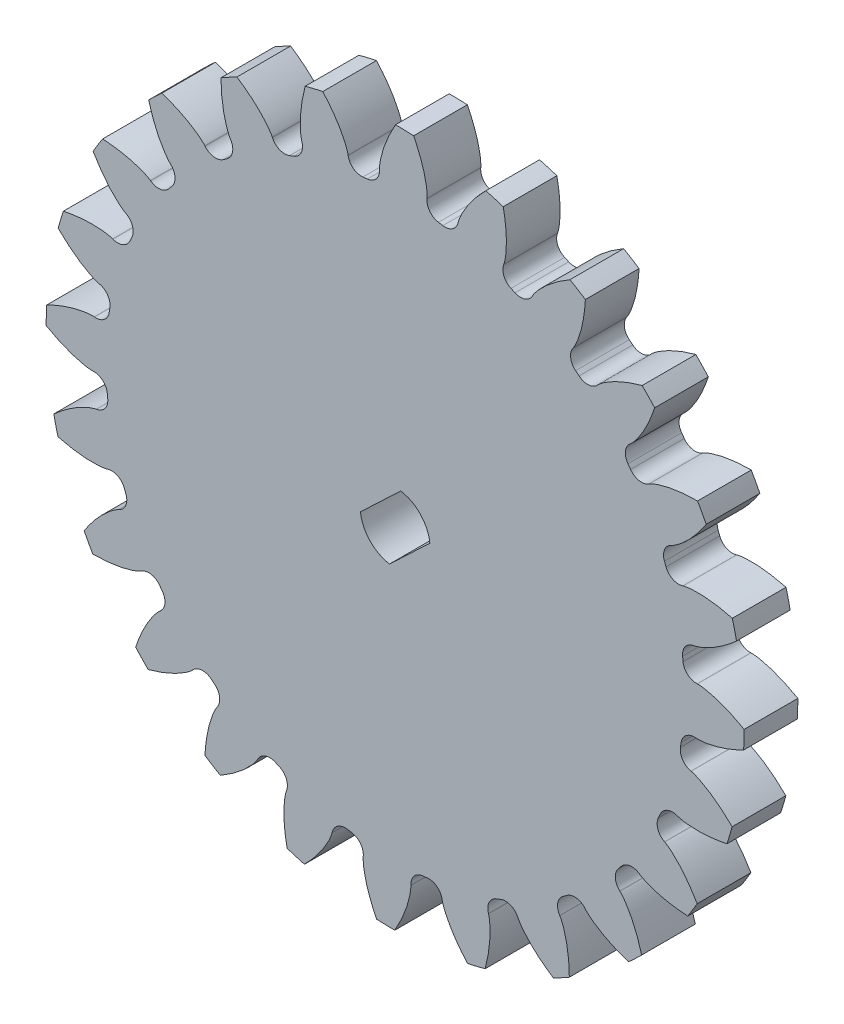
SolidWorks part; units mm, degrees
ref_plane "Plano frontal" through (0, 0, 0) normal (0, 0, 1) x (1, 0, 0)
ref_plane "Plano superior" through (0, 0, 0) normal (0, 1, 0) x (1, 0, 0)
ref_plane "Plano direito" through (0, 0, 0) normal (1, 0, 0) x (0, 0, -1)
sketch "Model" plane through (0, 0, 0) normal (0, 0, 1) x (1, 0, 0)
  line L0 (-21.0216, 0.4198) -> (-21.0462, 0.4292)
  line L1 (-22.0572, -2.974) -> (-22.0314, -2.9795)
  line L2 (-22.4004, -5.2968) -> (-22.4266, -5.2941)
  line L3 (-22.5224, -8.843) -> (-22.496, -8.8417)
  line L4 (-22.2526, -11.1755) -> (-22.2787, -11.1796)
  line L5 (-21.4526, -14.6324) -> (-21.4275, -14.6243)
  line L6 (-20.5884, -16.8156) -> (-20.6125, -16.8263)
  line L7 (-18.9209, -19.9477) -> (-18.8988, -19.9334)
  line L8 (-17.5211, -21.8328) -> (-17.5416, -21.8494)
  line L9 (-15.0998, -24.4266) -> (-15.0821, -24.407)
  line L10 (-13.2597, -25.8852) -> (-13.2752, -25.9065)
  line L11 (-10.2496, -27.7639) -> (-10.2376, -27.7404)
  line L12 (-8.0948, -28.6966) -> (-8.1042, -28.7212)
  line L13 (-4.701, -29.7322) -> (-4.6955, -29.7064)
  line L14 (-2.3782, -30.0754) -> (-2.3809, -30.1016)
  line L15 (1.168, -30.1974) -> (1.1667, -30.171)
  line L16 (3.5005, -29.9276) -> (3.5046, -29.9537)
  line L17 (6.9574, -29.1276) -> (6.9493, -29.1025)
  line L18 (9.1406, -28.2634) -> (9.1513, -28.2875)
  line L19 (12.2727, -26.5959) -> (12.2584, -26.5738)
  line L20 (14.1578, -25.1961) -> (14.1744, -25.2166)
  line L21 (16.7516, -22.7748) -> (16.732, -22.7571)
  line L22 (18.2102, -20.9347) -> (18.2315, -20.9502)
  line L23 (20.0889, -17.9246) -> (20.0654, -17.9126)
  line L24 (21.0216, -15.7698) -> (21.0462, -15.7792)
  line L25 (22.0572, -12.376) -> (22.0314, -12.3705)
  line L26 (22.4004, -10.0532) -> (22.4266, -10.0559)
  line L27 (22.5224, -6.507) -> (22.496, -6.5083)
  line L28 (22.2526, -4.1745) -> (22.2787, -4.1704)
  line L29 (21.4526, -0.7176) -> (21.4275, -0.7257)
  line L30 (20.5884, 1.4656) -> (20.6125, 1.4763)
  line L31 (18.9209, 4.5977) -> (18.8988, 4.5834)
  line L32 (17.5211, 6.4828) -> (17.5416, 6.4994)
  line L33 (15.0998, 9.0766) -> (15.0821, 9.057)
  line L34 (13.2597, 10.5352) -> (13.2752, 10.5565)
  line L35 (10.2496, 12.4139) -> (10.2376, 12.3904)
  line L36 (8.0948, 13.3466) -> (8.1042, 13.3712)
  line L37 (4.701, 14.3822) -> (4.6955, 14.3564)
  line L38 (2.3782, 14.7254) -> (2.3809, 14.7516)
  line L39 (-1.168, 14.8474) -> (-1.1667, 14.821)
  line L40 (-3.5005, 14.5776) -> (-3.5046, 14.6037)
  line L41 (-6.9574, 13.7776) -> (-6.9493, 13.7525)
  line L42 (-9.1406, 12.9134) -> (-9.1513, 12.9375)
  line L43 (-12.2727, 11.2459) -> (-12.2584, 11.2238)
  line L44 (-14.1578, 9.8461) -> (-14.1744, 9.8666)
  line L45 (-16.7516, 7.4248) -> (-16.732, 7.4071)
  line L46 (-18.2102, 5.5847) -> (-18.2315, 5.6002)
  line L47 (-20.0889, 2.5746) -> (-20.0654, 2.5626)
  line L48 (-0.4184, -10.2411) -> (2.5849, -7.3956)
  line L49 (0.4184, -5.1089) -> (-2.5849, -7.9544)
  arc A0 (-19.6106, 1.2577) -> (-19.7466, 0.9529) centre (0, -7.675) ccw
  arc A1 (-21.0216, 0.4198) -> (-19.7466, 0.9529) centre (-20.6629, 1.3533) ccw
  arc A2 (-24.7228, 0.3737) -> (-25.1072, -0.9201) centre (0, -7.675) ccw
  arc A3 (-21.2543, -4.1223) -> (-22.0314, -2.9795) centre (-22.2406, -3.9574) ccw
  arc A4 (-21.2543, -4.1223) -> (-21.3068, -4.4519) centre (0, -7.675) ccw
  arc A5 (-22.4004, -5.2968) -> (-21.3068, -4.4519) centre (-22.2955, -4.3023) ccw
  arc A6 (-25.9636, -6.2993) -> (-26, -7.6485) centre (0, -7.675) ccw
  arc A7 (-21.4496, -9.7443) -> (-22.496, -8.8417) centre (-22.445, -9.8404) ccw
  arc A8 (-21.4496, -9.7443) -> (-21.415, -10.0763) centre (0, -7.675) ccw
  arc A9 (-22.2526, -11.1755) -> (-21.415, -10.0763) centre (-22.4088, -10.1878) ccw
  arc A10 (-25.435, -13.066) -> (-25.1209, -14.3787) centre (0, -7.675) ccw
  arc A11 (-20.1832, -15.2254) -> (-21.4275, -14.6243) centre (-21.1198, -15.5758) ccw
  arc A12 (-20.1832, -15.2254) -> (-20.0638, -15.5371) centre (0, -7.675) ccw
  arc A13 (-20.5884, -16.8156) -> (-20.0638, -15.5371) centre (-20.9948, -15.902) ccw
  arc A14 (-23.173, -19.4654) -> (-22.5299, -20.652) centre (0, -7.675) ccw
  arc A15 (-17.5412, -20.1919) -> (-18.8988, -19.9334) centre (-18.3552, -20.7728) ccw
  arc A16 (-17.5412, -20.1919) -> (-17.3453, -20.4621) centre (0, -7.675) ccw
  arc A17 (-17.5211, -21.8328) -> (-17.3453, -20.4621) centre (-18.1502, -21.0555) ccw
  arc A18 (-19.3318, -25.0613) -> (-18.4035, -26.041) centre (0, -7.675) ccw
  arc A19 (-13.7039, -24.3054) -> (-15.0821, -24.407) centre (-14.3399, -25.0772) ccw
  arc A20 (-13.7039, -24.3054) -> (-13.4447, -24.5157) centre (0, -7.675) ccw
  arc A21 (-13.2597, -25.8852) -> (-13.4447, -24.5157) centre (-14.0686, -25.2972) ccw
  arc A22 (-14.1732, -29.4723) -> (-13.0229, -30.1784) centre (0, -7.675) ccw
  arc A23 (-8.9327, -27.2856) -> (-10.2376, -27.7404) centre (-9.3472, -28.1956) ccw
  arc A24 (-8.9327, -27.2856) -> (-8.6279, -27.4216) centre (0, -7.675) ccw
  arc A25 (-8.0948, -28.6966) -> (-8.6279, -27.4216) centre (-9.0283, -28.3379) ccw
  arc A26 (-8.0487, -32.3978) -> (-6.7549, -32.7822) centre (0, -7.675) ccw
  arc A27 (-3.5527, -28.9293) -> (-4.6955, -29.7064) centre (-3.7176, -29.9156) ccw
  arc A28 (-3.5527, -28.9293) -> (-3.2231, -28.9818) centre (0, -7.675) ccw
  arc A29 (-2.3782, -30.0754) -> (-3.2231, -28.9818) centre (-3.3727, -29.9705) ccw
  arc A30 (-1.3757, -33.6386) -> (-0.0265, -33.675) centre (0, -7.675) ccw
  arc A31 (2.0693, -29.1246) -> (1.1667, -30.171) centre (2.1654, -30.12) ccw
  arc A32 (2.0693, -29.1246) -> (2.4013, -29.09) centre (0, -7.675) ccw
  arc A33 (3.5005, -29.9276) -> (2.4013, -29.09) centre (2.5128, -30.0838) ccw
  arc A34 (5.391, -33.11) -> (6.7037, -32.7959) centre (0, -7.675) ccw
  arc A35 (7.5504, -27.8581) -> (6.9493, -29.1025) centre (7.9008, -28.7948) ccw
  arc A36 (7.5504, -27.8581) -> (7.8621, -27.7388) centre (0, -7.675) ccw
  arc A37 (9.1406, -28.2634) -> (7.8621, -27.7388) centre (8.227, -28.6698) ccw
  arc A38 (11.7904, -30.848) -> (12.977, -30.2049) centre (0, -7.675) ccw
  arc A39 (12.5169, -25.2162) -> (12.2584, -26.5738) centre (13.0978, -26.0302) ccw
  arc A40 (12.5169, -25.2162) -> (12.7871, -25.0203) centre (0, -7.675) ccw
  arc A41 (14.1578, -25.1961) -> (12.7871, -25.0203) centre (13.3805, -25.8252) ccw
  arc A42 (17.3863, -27.0068) -> (18.366, -26.0785) centre (0, -7.675) ccw
  arc A43 (16.6304, -21.3789) -> (16.732, -22.7571) centre (17.4022, -22.0149) ccw
  arc A44 (16.6304, -21.3789) -> (16.8407, -21.1197) centre (0, -7.675) ccw
  arc A45 (18.2102, -20.9347) -> (16.8407, -21.1197) centre (17.6222, -21.7436) ccw
  arc A46 (21.7973, -21.8482) -> (22.5034, -20.6979) centre (0, -7.675) ccw
  arc A47 (19.6106, -16.6077) -> (20.0654, -17.9126) centre (20.5206, -17.0222) ccw
  arc A48 (19.6106, -16.6077) -> (19.7466, -16.3029) centre (0, -7.675) ccw
  arc A49 (21.0216, -15.7698) -> (19.7466, -16.3029) centre (20.6629, -16.7033) ccw
  arc A50 (24.7228, -15.7237) -> (25.1072, -14.4299) centre (0, -7.675) ccw
  arc A51 (21.2543, -11.2277) -> (22.0314, -12.3705) centre (22.2406, -11.3926) ccw
  arc A52 (21.2543, -11.2277) -> (21.3068, -10.8981) centre (0, -7.675) ccw
  arc A53 (22.4004, -10.0532) -> (21.3068, -10.8981) centre (22.2955, -11.0477) ccw
  arc A54 (25.9636, -9.0507) -> (26, -7.7015) centre (0, -7.675) ccw
  arc A55 (21.4496, -5.6057) -> (22.496, -6.5083) centre (22.445, -5.5096) ccw
  arc A56 (21.4496, -5.6057) -> (21.415, -5.2737) centre (0, -7.675) ccw
  arc A57 (22.2526, -4.1745) -> (21.415, -5.2737) centre (22.4088, -5.1622) ccw
  arc A58 (25.435, -2.284) -> (25.1209, -0.9713) centre (0, -7.675) ccw
  arc A59 (20.1832, -0.1246) -> (21.4275, -0.7257) centre (21.1198, 0.2258) ccw
  arc A60 (20.1832, -0.1246) -> (20.0638, 0.1871) centre (0, -7.675) ccw
  arc A61 (20.5884, 1.4656) -> (20.0638, 0.1871) centre (20.9948, 0.552) ccw
  arc A62 (23.173, 4.1154) -> (22.5299, 5.302) centre (0, -7.675) ccw
  arc A63 (17.5412, 4.8419) -> (18.8988, 4.5834) centre (18.3552, 5.4228) ccw
  arc A64 (17.5412, 4.8419) -> (17.3453, 5.1121) centre (0, -7.675) ccw
  arc A65 (17.5211, 6.4828) -> (17.3453, 5.1121) centre (18.1502, 5.7055) ccw
  arc A66 (19.3318, 9.7113) -> (18.4035, 10.691) centre (0, -7.675) ccw
  arc A67 (13.7039, 8.9554) -> (15.0821, 9.057) centre (14.3399, 9.7272) ccw
  arc A68 (13.7039, 8.9554) -> (13.4447, 9.1657) centre (0, -7.675) ccw
  arc A69 (13.2597, 10.5352) -> (13.4447, 9.1657) centre (14.0686, 9.9472) ccw
  arc A70 (14.1732, 14.1223) -> (13.0229, 14.8284) centre (0, -7.675) ccw
  arc A71 (8.9327, 11.9356) -> (10.2376, 12.3904) centre (9.3472, 12.8456) ccw
  arc A72 (8.9327, 11.9356) -> (8.6279, 12.0716) centre (0, -7.675) ccw
  arc A73 (8.0948, 13.3466) -> (8.6279, 12.0716) centre (9.0283, 12.9879) ccw
  arc A74 (8.0487, 17.0478) -> (6.7549, 17.4322) centre (0, -7.675) ccw
  arc A75 (3.5527, 13.5793) -> (4.6955, 14.3564) centre (3.7176, 14.5656) ccw
  arc A76 (3.5527, 13.5793) -> (3.2231, 13.6318) centre (0, -7.675) ccw
  arc A77 (2.3782, 14.7254) -> (3.2231, 13.6318) centre (3.3727, 14.6206) ccw
  arc A78 (1.3757, 18.2886) -> (0.0265, 18.325) centre (0, -7.675) ccw
  arc A79 (-2.0693, 13.7746) -> (-1.1667, 14.821) centre (-2.1654, 14.77) ccw
  arc A80 (-2.0693, 13.7746) -> (-2.4013, 13.74) centre (0, -7.675) ccw
  arc A81 (-3.5005, 14.5776) -> (-2.4013, 13.74) centre (-2.5128, 14.7338) ccw
  arc A82 (-5.391, 17.76) -> (-6.7037, 17.4459) centre (0, -7.675) ccw
  arc A83 (-7.5504, 12.5082) -> (-6.9493, 13.7525) centre (-7.9008, 13.4448) ccw
  arc A84 (-7.5504, 12.5082) -> (-7.8621, 12.3888) centre (0, -7.675) ccw
  arc A85 (-9.1406, 12.9134) -> (-7.8621, 12.3888) centre (-8.227, 13.3198) ccw
  arc A86 (-11.7904, 15.498) -> (-12.977, 14.8549) centre (0, -7.675) ccw
  arc A87 (-12.5169, 9.8662) -> (-12.2584, 11.2238) centre (-13.0978, 10.6802) ccw
  arc A88 (-12.5169, 9.8662) -> (-12.7871, 9.6703) centre (0, -7.675) ccw
  arc A89 (-14.1578, 9.8461) -> (-12.7871, 9.6703) centre (-13.3805, 10.4752) ccw
  arc A90 (-17.3863, 11.6568) -> (-18.366, 10.7285) centre (0, -7.675) ccw
  arc A91 (-16.6304, 6.0289) -> (-16.732, 7.4071) centre (-17.4022, 6.6649) ccw
  arc A92 (-16.6304, 6.0289) -> (-16.8407, 5.7697) centre (0, -7.675) ccw
  arc A93 (-18.2102, 5.5847) -> (-16.8407, 5.7697) centre (-17.6222, 6.3936) ccw
  arc A94 (-21.7973, 6.4982) -> (-22.5034, 5.3479) centre (0, -7.675) ccw
  arc A95 (-19.6106, 1.2577) -> (-20.0654, 2.5626) centre (-20.5206, 1.6722) ccw
  arc A96 (2.5849, -7.3956) -> (0.4184, -5.1089) centre (0, -7.675) ccw
  arc A97 (-2.5849, -7.9544) -> (-0.4184, -10.2411) centre (0, -7.675) ccw
  spline S0 degree 5 number of poles 75 (-21.0462, 0.4292) -> (-24.7228, 0.3737)
  spline S1 degree 5 number of poles 75 (-22.0572, -2.974) -> (-25.1072, -0.9201)
  spline S2 degree 5 number of poles 75 (-22.4266, -5.2941) -> (-25.9636, -6.2993)
  spline S3 degree 5 number of poles 75 (-22.5224, -8.843) -> (-26, -7.6485)
  spline S4 degree 5 number of poles 75 (-22.2787, -11.1796) -> (-25.435, -13.066)
  spline S5 degree 5 number of poles 75 (-21.4526, -14.6324) -> (-25.1209, -14.3787)
  spline S6 degree 5 number of poles 75 (-20.6125, -16.8263) -> (-23.173, -19.4654)
  spline S7 degree 5 number of poles 75 (-18.9209, -19.9477) -> (-22.5299, -20.652)
  spline S8 degree 5 number of poles 75 (-17.5416, -21.8494) -> (-19.3318, -25.0613)
  spline S9 degree 5 number of poles 75 (-15.0998, -24.4266) -> (-18.4035, -26.041)
  spline S10 degree 5 number of poles 75 (-13.2752, -25.9065) -> (-14.1732, -29.4723)
  spline S11 degree 5 number of poles 75 (-10.2496, -27.7639) -> (-13.0229, -30.1784)
  spline S12 degree 5 number of poles 75 (-8.1042, -28.7212) -> (-8.0487, -32.3978)
  spline S13 degree 5 number of poles 75 (-4.701, -29.7322) -> (-6.7549, -32.7822)
  spline S14 degree 5 number of poles 75 (-2.3809, -30.1016) -> (-1.3757, -33.6386)
  spline S15 degree 5 number of poles 75 (1.168, -30.1974) -> (-0.0265, -33.675)
  spline S16 degree 5 number of poles 75 (3.5046, -29.9537) -> (5.391, -33.11)
  spline S17 degree 5 number of poles 75 (6.9574, -29.1276) -> (6.7037, -32.7959)
  spline S18 degree 5 number of poles 75 (9.1513, -28.2875) -> (11.7904, -30.848)
  spline S19 degree 5 number of poles 75 (12.2727, -26.5959) -> (12.977, -30.2049)
  spline S20 degree 5 number of poles 75 (14.1744, -25.2166) -> (17.3863, -27.0068)
  spline S21 degree 5 number of poles 75 (16.7516, -22.7748) -> (18.366, -26.0785)
  spline S22 degree 5 number of poles 75 (18.2315, -20.9502) -> (21.7973, -21.8482)
  spline S23 degree 5 number of poles 75 (20.0889, -17.9246) -> (22.5034, -20.6979)
  spline S24 degree 5 number of poles 75 (21.0462, -15.7792) -> (24.7228, -15.7237)
  spline S25 degree 5 number of poles 75 (22.0572, -12.376) -> (25.1072, -14.4299)
  spline S26 degree 5 number of poles 75 (22.4266, -10.0559) -> (25.9636, -9.0507)
  spline S27 degree 5 number of poles 75 (22.5224, -6.507) -> (26, -7.7015)
  spline S28 degree 5 number of poles 75 (22.2787, -4.1704) -> (25.435, -2.284)
  spline S29 degree 5 number of poles 75 (21.4526, -0.7176) -> (25.1209, -0.9713)
  spline S30 degree 5 number of poles 75 (20.6125, 1.4763) -> (23.173, 4.1154)
  spline S31 degree 5 number of poles 75 (18.9209, 4.5977) -> (22.5299, 5.302)
  spline S32 degree 5 number of poles 75 (17.5416, 6.4994) -> (19.3318, 9.7113)
  spline S33 degree 5 number of poles 75 (15.0998, 9.0766) -> (18.4035, 10.691)
  spline S34 degree 5 number of poles 75 (13.2752, 10.5565) -> (14.1732, 14.1223)
  spline S35 degree 5 number of poles 75 (10.2496, 12.4139) -> (13.0229, 14.8284)
  spline S36 degree 5 number of poles 75 (8.1042, 13.3712) -> (8.0487, 17.0478)
  spline S37 degree 5 number of poles 75 (4.701, 14.3822) -> (6.7549, 17.4322)
  spline S38 degree 5 number of poles 75 (2.3809, 14.7516) -> (1.3757, 18.2886)
  spline S39 degree 5 number of poles 75 (-1.168, 14.8474) -> (0.0265, 18.325)
  spline S40 degree 5 number of poles 75 (-3.5046, 14.6037) -> (-5.391, 17.76)
  spline S41 degree 5 number of poles 75 (-6.9574, 13.7776) -> (-6.7037, 17.4459)
  spline S42 degree 5 number of poles 75 (-9.1513, 12.9375) -> (-11.7904, 15.498)
  spline S43 degree 5 number of poles 75 (-12.2727, 11.2459) -> (-12.977, 14.8549)
  spline S44 degree 5 number of poles 75 (-14.1744, 9.8666) -> (-17.3863, 11.6568)
  spline S45 degree 5 number of poles 75 (-16.7516, 7.4248) -> (-18.366, 10.7285)
  spline S46 degree 5 number of poles 75 (-18.2315, 5.6002) -> (-21.7973, 6.4982)
  spline S47 degree 5 number of poles 75 (-20.0889, 2.5746) -> (-22.5034, 5.3479)
extrude "Ressalto-extrusão1" add sketch "Model" along normal blind 4
